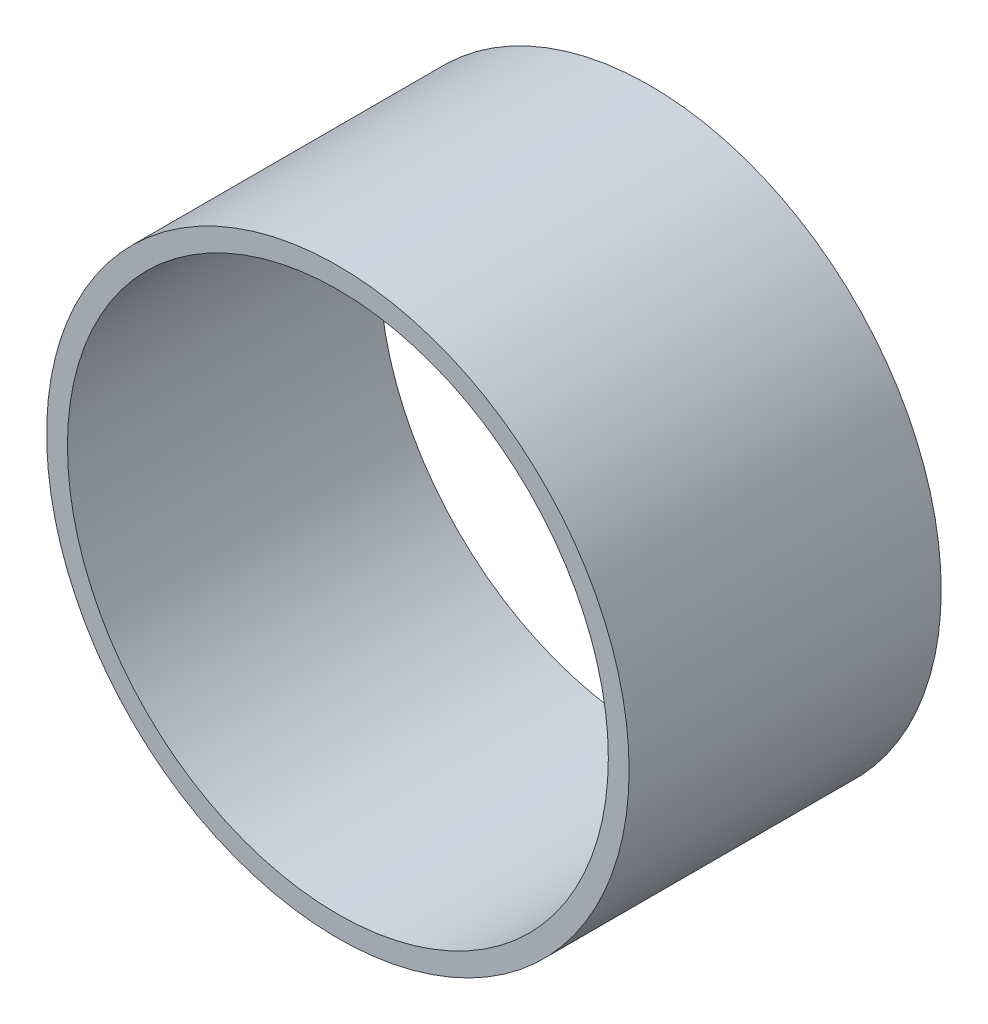
SolidWorks part; units mm, degrees
material "AISI 316 Stainless Steel Sheet (SS)"
ref_plane "Front Plane" through (0, 0, 0) normal (0, 0, 1) x (1, 0, 0)
ref_plane "Top Plane" through (0, 0, 0) normal (0, 1, 0) x (1, 0, 0)
ref_plane "Right Plane" through (0, 0, 0) normal (1, 0, 0) x (0, 0, -1)
sketch "Sketch1" plane through (0, 0, 0) normal (0, 0, 1) x (1, 0, 0)
  circle A0 centre (0, 0) radius 13
  circle A1 centre (0, 0) radius 14
extrude "Boss-Extrude1" add sketch "Sketch1" along normal blind 15
